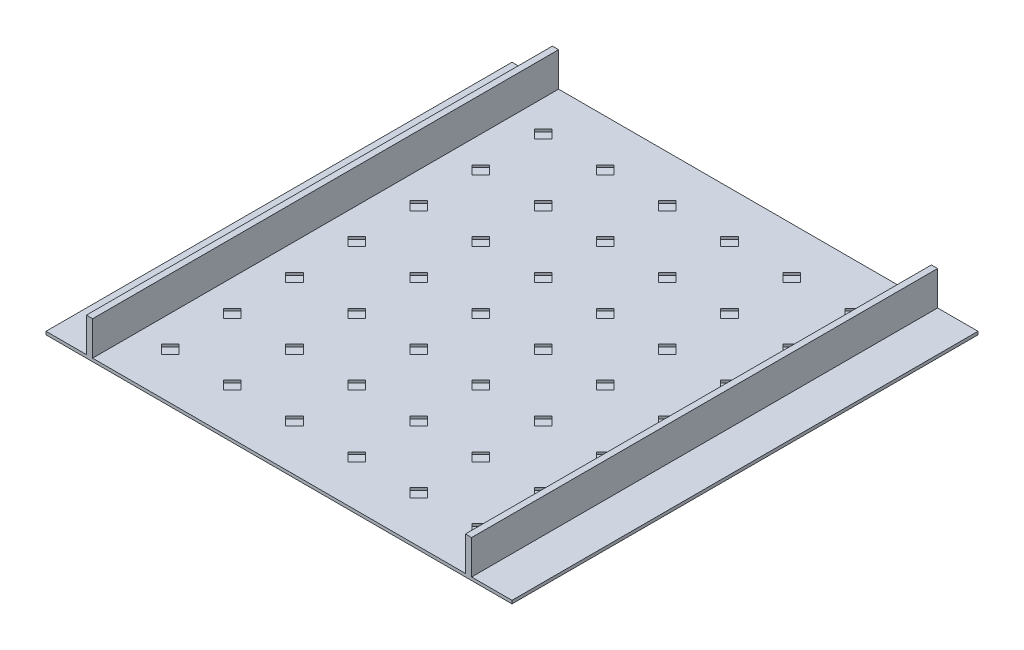
SolidWorks part; units mm, degrees
ref_plane "Front Plane" through (0, 0, 0) normal (0, 0, 1) x (1, 0, 0)
ref_plane "Top Plane" through (0, 0, 0) normal (0, 1, 0) x (1, 0, 0)
ref_plane "Right Plane" through (0, 0, 0) normal (1, 0, 0) x (0, 0, -1)
sketch "Sketch2" plane through (0, 0, 0) normal (0, 1, 0) x (1, 0, 0)
  line L1 (-750, 750) -> (750, 750)
  line L2 (-750, 750) -> (-750, -750)
  line L3 (-750, -750) -> (750, -750)
  line L4 (750, 750) -> (750, -750)
  line L5 (-750, 750) -> (750, -750) construction
  line L6 (-750, -750) -> (750, 750) construction
  point P0 (0, 0)
  dimension "D1" = 1500
  dimension "D2" = 1500
extrude "Boss-Extrude1" add sketch "Sketch2" along normal blind 10
sketch "Sketch3" plane through (0, 10, 0) normal (0, 1, 0) x (1, 0, 0)
  line L0 (620, 750) -> (620, -750) construction
  line L1 (750, 750) -> (-750, 750) construction
  line L2 (-750, -750) -> (750, -750) construction
  line L3 (600, 750) -> (600, -750) construction
  line L4 (750, -750) -> (750, 750) construction
  line L5 (-750, -600) -> (750, -600) construction
  line L6 (-750, 750) -> (-750, -750) construction
  line L7 (-750, -620) -> (750, -620) construction
  line L8 (-750, 0) -> (750, 0) construction
  line L9 (0, 750) -> (0, -750) construction
  line L10 (-750, 620) -> (750, 620) construction
  line L11 (-750, 600) -> (750, 600) construction
  line L12 (-620, 750) -> (-620, -750) construction
  line L13 (-600, 750) -> (-600, -750) construction
  line L15 (-620, 750) -> (-600, 750)
  line L16 (-620, 750) -> (-620, -750)
  line L17 (-620, -750) -> (-600, -750)
  line L18 (-600, 750) -> (-600, -750)
  line L19 (600, 750) -> (620, 750)
  line L20 (600, 750) -> (600, -750)
  line L21 (600, -750) -> (620, -750)
  line L22 (620, 750) -> (620, -750)
  dimension "D6" = 150
  dimension "D5" = 20
  dimension "D7" = 20
  dimension "D8" = 150
extrude "Boss-Extrude2" add sketch "Sketch3" along normal blind 110
sketch "Sketch4" plane through (0, 10, 0) normal (0, 1, 0) x (1, 0, 0)
  line L0 (-500, 628.2843) -> (-471.7157, 600)
  line L1 (-500, 628.2843) -> (-528.2843, 600)
  line L2 (-471.7157, 600) -> (-500, 571.7157)
  line L3 (-528.2843, 600) -> (-500, 571.7157)
  line L4 (-500, 628.2843) -> (-500, 571.7157) construction
  line L5 (-471.7157, 600) -> (-528.2843, 600) construction
  line L6 (-300, 628.2843) -> (-271.7157, 600)
  line L7 (-300, 628.2843) -> (-328.2843, 600)
  line L8 (-271.7157, 600) -> (-300, 571.7157)
  line L9 (-328.2843, 600) -> (-300, 571.7157)
  line L10 (-300, 628.2843) -> (-300, 571.7157) construction
  line L11 (-271.7157, 600) -> (-328.2843, 600) construction
  line L12 (-100, 628.2843) -> (-71.7157, 600)
  line L13 (-100, 628.2843) -> (-128.2843, 600)
  line L14 (-71.7157, 600) -> (-100, 571.7157)
  line L15 (-128.2843, 600) -> (-100, 571.7157)
  line L16 (-100, 628.2843) -> (-100, 571.7157) construction
  line L17 (-71.7157, 600) -> (-128.2843, 600) construction
  line L18 (100, 628.2843) -> (128.2843, 600)
  line L19 (100, 628.2843) -> (71.7157, 600)
  line L20 (128.2843, 600) -> (100, 571.7157)
  line L21 (71.7157, 600) -> (100, 571.7157)
  line L22 (100, 628.2843) -> (100, 571.7157) construction
  line L23 (128.2843, 600) -> (71.7157, 600) construction
  line L24 (300, 628.2843) -> (328.2843, 600)
  line L25 (300, 628.2843) -> (271.7157, 600)
  line L26 (328.2843, 600) -> (300, 571.7157)
  line L27 (271.7157, 600) -> (300, 571.7157)
  line L28 (300, 628.2843) -> (300, 571.7157) construction
  line L29 (328.2843, 600) -> (271.7157, 600) construction
  line L30 (500, 628.2843) -> (528.2843, 600)
  line L31 (500, 628.2843) -> (471.7157, 600)
  line L32 (528.2843, 600) -> (500, 571.7157)
  line L33 (471.7157, 600) -> (500, 571.7157)
  line L34 (500, 628.2843) -> (500, 571.7157) construction
  line L35 (528.2843, 600) -> (471.7157, 600) construction
  line L36 (-300, 428.2843) -> (-271.7157, 400)
  line L37 (-300, 428.2843) -> (-328.2843, 400)
  line L38 (-271.7157, 400) -> (-300, 371.7157)
  line L39 (-328.2843, 400) -> (-300, 371.7157)
  line L40 (-300, 428.2843) -> (-300, 371.7157) construction
  line L41 (-271.7157, 400) -> (-328.2843, 400) construction
  line L42 (-100, 428.2843) -> (-71.7157, 400)
  line L43 (-100, 428.2843) -> (-128.2843, 400)
  line L44 (-71.7157, 400) -> (-100, 371.7157)
  line L45 (-128.2843, 400) -> (-100, 371.7157)
  line L46 (-100, 428.2843) -> (-100, 371.7157) construction
  line L47 (-71.7157, 400) -> (-128.2843, 400) construction
  line L48 (100, 428.2843) -> (128.2843, 400)
  line L49 (100, 428.2843) -> (71.7157, 400)
  line L50 (128.2843, 400) -> (100, 371.7157)
  line L51 (71.7157, 400) -> (100, 371.7157)
  line L52 (100, 428.2843) -> (100, 371.7157) construction
  line L53 (128.2843, 400) -> (71.7157, 400) construction
  line L54 (300, 428.2843) -> (328.2843, 400)
  line L55 (300, 428.2843) -> (271.7157, 400)
  line L56 (328.2843, 400) -> (300, 371.7157)
  line L57 (271.7157, 400) -> (300, 371.7157)
  line L58 (300, 428.2843) -> (300, 371.7157) construction
  line L59 (328.2843, 400) -> (271.7157, 400) construction
  line L60 (500, 428.2843) -> (528.2843, 400)
  line L61 (500, 428.2843) -> (471.7157, 400)
  line L62 (528.2843, 400) -> (500, 371.7157)
  line L63 (471.7157, 400) -> (500, 371.7157)
  line L64 (500, 428.2843) -> (500, 371.7157) construction
  line L65 (528.2843, 400) -> (471.7157, 400) construction
  line L66 (-300, 228.2843) -> (-271.7157, 200)
  line L67 (-300, 228.2843) -> (-328.2843, 200)
  line L68 (-271.7157, 200) -> (-300, 171.7157)
  line L69 (-328.2843, 200) -> (-300, 171.7157)
  line L70 (-300, 228.2843) -> (-300, 171.7157) construction
  line L71 (-271.7157, 200) -> (-328.2843, 200) construction
  line L72 (-100, 228.2843) -> (-71.7157, 200)
  line L73 (-100, 228.2843) -> (-128.2843, 200)
  line L74 (-71.7157, 200) -> (-100, 171.7157)
  line L75 (-128.2843, 200) -> (-100, 171.7157)
  line L76 (-100, 228.2843) -> (-100, 171.7157) construction
  line L77 (-71.7157, 200) -> (-128.2843, 200) construction
  line L78 (100, 228.2843) -> (128.2843, 200)
  line L79 (100, 228.2843) -> (71.7157, 200)
  line L80 (128.2843, 200) -> (100, 171.7157)
  line L81 (71.7157, 200) -> (100, 171.7157)
  line L82 (100, 228.2843) -> (100, 171.7157) construction
  line L83 (128.2843, 200) -> (71.7157, 200) construction
  line L84 (300, 228.2843) -> (328.2843, 200)
  line L85 (300, 228.2843) -> (271.7157, 200)
  line L86 (328.2843, 200) -> (300, 171.7157)
  line L87 (271.7157, 200) -> (300, 171.7157)
  line L88 (300, 228.2843) -> (300, 171.7157) construction
  line L89 (328.2843, 200) -> (271.7157, 200) construction
  line L90 (500, 228.2843) -> (528.2843, 200)
  line L91 (500, 228.2843) -> (471.7157, 200)
  line L92 (528.2843, 200) -> (500, 171.7157)
  line L93 (471.7157, 200) -> (500, 171.7157)
  line L94 (500, 228.2843) -> (500, 171.7157) construction
  line L95 (528.2843, 200) -> (471.7157, 200) construction
  line L96 (-300, 28.2843) -> (-271.7157, 0)
  line L97 (-300, 28.2843) -> (-328.2843, 0)
  line L98 (-271.7157, 0) -> (-300, -28.2843)
  line L99 (-328.2843, 0) -> (-300, -28.2843)
  line L100 (-300, 28.2843) -> (-300, -28.2843) construction
  line L101 (-271.7157, 0) -> (-328.2843, 0) construction
  line L102 (-100, 28.2843) -> (-71.7157, 0)
  line L103 (-100, 28.2843) -> (-128.2843, 0)
  line L104 (-71.7157, 0) -> (-100, -28.2843)
  line L105 (-128.2843, 0) -> (-100, -28.2843)
  line L106 (-100, 28.2843) -> (-100, -28.2843) construction
  line L107 (-71.7157, 0) -> (-128.2843, 0) construction
  line L108 (100, 28.2843) -> (128.2843, 0)
  line L109 (100, 28.2843) -> (71.7157, 0)
  line L110 (128.2843, 0) -> (100, -28.2843)
  line L111 (71.7157, 0) -> (100, -28.2843)
  line L112 (100, 28.2843) -> (100, -28.2843) construction
  line L113 (128.2843, 0) -> (71.7157, 0) construction
  line L114 (300, 28.2843) -> (328.2843, 0)
  line L115 (300, 28.2843) -> (271.7157, 0)
  line L116 (328.2843, 0) -> (300, -28.2843)
  line L117 (271.7157, 0) -> (300, -28.2843)
  line L118 (300, 28.2843) -> (300, -28.2843) construction
  line L119 (328.2843, 0) -> (271.7157, 0) construction
  line L120 (500, 28.2843) -> (528.2843, 0)
  line L121 (500, 28.2843) -> (471.7157, 0)
  line L122 (528.2843, 0) -> (500, -28.2843)
  line L123 (471.7157, 0) -> (500, -28.2843)
  line L124 (500, 28.2843) -> (500, -28.2843) construction
  line L125 (528.2843, 0) -> (471.7157, 0) construction
  line L126 (-300, -171.7157) -> (-271.7157, -200)
  line L127 (-300, -171.7157) -> (-328.2843, -200)
  line L128 (-271.7157, -200) -> (-300, -228.2843)
  line L129 (-328.2843, -200) -> (-300, -228.2843)
  line L130 (-300, -171.7157) -> (-300, -228.2843) construction
  line L131 (-271.7157, -200) -> (-328.2843, -200) construction
  line L132 (-100, -171.7157) -> (-71.7157, -200)
  line L133 (-100, -171.7157) -> (-128.2843, -200)
  line L134 (-71.7157, -200) -> (-100, -228.2843)
  line L135 (-128.2843, -200) -> (-100, -228.2843)
  line L136 (-100, -171.7157) -> (-100, -228.2843) construction
  line L137 (-71.7157, -200) -> (-128.2843, -200) construction
  line L138 (100, -171.7157) -> (128.2843, -200)
  line L139 (100, -171.7157) -> (71.7157, -200)
  line L140 (128.2843, -200) -> (100, -228.2843)
  line L141 (71.7157, -200) -> (100, -228.2843)
  line L142 (100, -171.7157) -> (100, -228.2843) construction
  line L143 (128.2843, -200) -> (71.7157, -200) construction
  line L144 (300, -171.7157) -> (328.2843, -200)
  line L145 (300, -171.7157) -> (271.7157, -200)
  line L146 (328.2843, -200) -> (300, -228.2843)
  line L147 (271.7157, -200) -> (300, -228.2843)
  line L148 (300, -171.7157) -> (300, -228.2843) construction
  line L149 (328.2843, -200) -> (271.7157, -200) construction
  line L150 (500, -171.7157) -> (528.2843, -200)
  line L151 (500, -171.7157) -> (471.7157, -200)
  line L152 (528.2843, -200) -> (500, -228.2843)
  line L153 (471.7157, -200) -> (500, -228.2843)
  line L154 (500, -171.7157) -> (500, -228.2843) construction
  line L155 (528.2843, -200) -> (471.7157, -200) construction
  line L156 (-300, -371.7157) -> (-271.7157, -400)
  line L157 (-300, -371.7157) -> (-328.2843, -400)
  line L158 (-271.7157, -400) -> (-300, -428.2843)
  line L159 (-328.2843, -400) -> (-300, -428.2843)
  line L160 (-300, -371.7157) -> (-300, -428.2843) construction
  line L161 (-271.7157, -400) -> (-328.2843, -400) construction
  line L162 (-100, -371.7157) -> (-71.7157, -400)
  line L163 (-100, -371.7157) -> (-128.2843, -400)
  line L164 (-71.7157, -400) -> (-100, -428.2843)
  line L165 (-128.2843, -400) -> (-100, -428.2843)
  line L166 (-100, -371.7157) -> (-100, -428.2843) construction
  line L167 (-71.7157, -400) -> (-128.2843, -400) construction
  line L168 (100, -371.7157) -> (128.2843, -400)
  line L169 (100, -371.7157) -> (71.7157, -400)
  line L170 (128.2843, -400) -> (100, -428.2843)
  line L171 (71.7157, -400) -> (100, -428.2843)
  line L172 (100, -371.7157) -> (100, -428.2843) construction
  line L173 (128.2843, -400) -> (71.7157, -400) construction
  line L174 (300, -371.7157) -> (328.2843, -400)
  line L175 (300, -371.7157) -> (271.7157, -400)
  line L176 (328.2843, -400) -> (300, -428.2843)
  line L177 (271.7157, -400) -> (300, -428.2843)
  line L178 (300, -371.7157) -> (300, -428.2843) construction
  line L179 (328.2843, -400) -> (271.7157, -400) construction
  line L180 (500, -371.7157) -> (528.2843, -400)
  line L181 (500, -371.7157) -> (471.7157, -400)
  line L182 (528.2843, -400) -> (500, -428.2843)
  line L183 (471.7157, -400) -> (500, -428.2843)
  line L184 (500, -371.7157) -> (500, -428.2843) construction
  line L185 (528.2843, -400) -> (471.7157, -400) construction
  line L186 (-500, 428.2843) -> (-471.7157, 400)
  line L187 (-500, 428.2843) -> (-528.2843, 400)
  line L188 (-471.7157, 400) -> (-500, 371.7157)
  line L189 (-528.2843, 400) -> (-500, 371.7157)
  line L190 (-500, 428.2843) -> (-500, 371.7157) construction
  line L191 (-471.7157, 400) -> (-528.2843, 400) construction
  line L192 (-500, 228.2843) -> (-471.7157, 200)
  line L193 (-500, 228.2843) -> (-528.2843, 200)
  line L194 (-471.7157, 200) -> (-500, 171.7157)
  line L195 (-528.2843, 200) -> (-500, 171.7157)
  line L196 (-500, 228.2843) -> (-500, 171.7157) construction
  line L197 (-471.7157, 200) -> (-528.2843, 200) construction
  line L198 (-500, 28.2843) -> (-471.7157, 0)
  line L199 (-500, 28.2843) -> (-528.2843, 0)
  line L200 (-471.7157, 0) -> (-500, -28.2843)
  line L201 (-528.2843, 0) -> (-500, -28.2843)
  line L202 (-500, 28.2843) -> (-500, -28.2843) construction
  line L203 (-471.7157, 0) -> (-528.2843, 0) construction
  line L204 (-500, -171.7157) -> (-471.7157, -200)
  line L205 (-500, -171.7157) -> (-528.2843, -200)
  line L206 (-471.7157, -200) -> (-500, -228.2843)
  line L207 (-528.2843, -200) -> (-500, -228.2843)
  line L208 (-500, -171.7157) -> (-500, -228.2843) construction
  line L209 (-471.7157, -200) -> (-528.2843, -200) construction
  line L210 (-500, -371.7157) -> (-471.7157, -400)
  line L211 (-500, -371.7157) -> (-528.2843, -400)
  line L212 (-471.7157, -400) -> (-500, -428.2843)
  line L213 (-528.2843, -400) -> (-500, -428.2843)
  line L214 (-500, -371.7157) -> (-500, -428.2843) construction
  line L215 (-471.7157, -400) -> (-528.2843, -400) construction
  line L216 (0, 750) -> (0, -750) construction
  line L217 (600, 750) -> (-600, 750) construction
  line L218 (-600, -750) -> (600, -750) construction
  line L219 (-750, 0) -> (750, 0) construction
  line L220 (-750, 750) -> (-750, -750) construction
  line L221 (750, -750) -> (750, 750) construction
  line L222 (-100, 600) -> (100, 600) construction
  line L223 (-100, -400) -> (100, -400) construction
  line L224 (0, -400) -> (0, 600) construction
  line L225 (-500, -571.7157) -> (-471.7157, -600)
  line L226 (-500, -571.7157) -> (-528.2843, -600)
  line L227 (-471.7157, -600) -> (-500, -628.2843)
  line L228 (-528.2843, -600) -> (-500, -628.2843)
  line L229 (-500, -571.7157) -> (-500, -628.2843) construction
  line L230 (-471.7157, -600) -> (-528.2843, -600) construction
  line L231 (-300, -571.7157) -> (-271.7157, -600)
  line L232 (-300, -571.7157) -> (-328.2843, -600)
  line L233 (-271.7157, -600) -> (-300, -628.2843)
  line L234 (-328.2843, -600) -> (-300, -628.2843)
  line L235 (-300, -571.7157) -> (-300, -628.2843) construction
  line L236 (-271.7157, -600) -> (-328.2843, -600) construction
  line L237 (-100, -571.7157) -> (-71.7157, -600)
  line L238 (-100, -571.7157) -> (-128.2843, -600)
  line L239 (-71.7157, -600) -> (-100, -628.2843)
  line L240 (-128.2843, -600) -> (-100, -628.2843)
  line L241 (-100, -571.7157) -> (-100, -628.2843) construction
  line L242 (-71.7157, -600) -> (-128.2843, -600) construction
  line L243 (100, -571.7157) -> (128.2843, -600)
  line L244 (100, -571.7157) -> (71.7157, -600)
  line L245 (128.2843, -600) -> (100, -628.2843)
  line L246 (71.7157, -600) -> (100, -628.2843)
  line L247 (100, -571.7157) -> (100, -628.2843) construction
  line L248 (128.2843, -600) -> (71.7157, -600) construction
  line L249 (300, -571.7157) -> (328.2843, -600)
  line L250 (300, -571.7157) -> (271.7157, -600)
  line L251 (328.2843, -600) -> (300, -628.2843)
  line L252 (271.7157, -600) -> (300, -628.2843)
  line L253 (300, -571.7157) -> (300, -628.2843) construction
  line L254 (328.2843, -600) -> (271.7157, -600) construction
  line L255 (500, -571.7157) -> (528.2843, -600)
  line L256 (500, -571.7157) -> (471.7157, -600)
  line L257 (528.2843, -600) -> (500, -628.2843)
  line L258 (471.7157, -600) -> (500, -628.2843)
  line L259 (500, -571.7157) -> (500, -628.2843) construction
  line L260 (528.2843, -600) -> (471.7157, -600) construction
  point P1 (-500, 600)
  point P3 (-300, 600)
  point P12 (-100, 600)
  point P17 (100, 600)
  point P22 (300, 600)
  point P27 (500, 600)
  point P32 (-300, 400)
  point P37 (-100, 400)
  point P42 (100, 400)
  point P47 (300, 400)
  point P52 (500, 400)
  point P57 (-300, 200)
  point P62 (-100, 200)
  point P67 (100, 200)
  point P72 (300, 200)
  point P77 (500, 200)
  point P82 (-300, 0)
  point P87 (-100, 0)
  point P92 (100, 0)
  point P97 (300, 0)
  point P102 (500, 0)
  point P107 (-300, -200)
  point P112 (-100, -200)
  point P117 (100, -200)
  point P122 (300, -200)
  point P127 (500, -200)
  point P132 (-300, -400)
  point P137 (-100, -400)
  point P142 (100, -400)
  point P147 (300, -400)
  point P152 (500, -400)
  point P157 (-500, 400)
  point P162 (-500, 200)
  point P167 (-500, 0)
  point P172 (-500, -200)
  point P177 (-500, -400)
  point P198 (-500, -600)
  point P205 (-300, -600)
  point P210 (-100, -600)
  point P215 (100, -600)
  point P220 (300, -600)
  point P225 (500, -600)
  dimension "D1" = 40
  dimension "D2" = 40
  dimension "D5" = 200
  dimension "D6" = 200
  dimension "D3" = 6
  dimension "D4" = 7
extrude "Cut-Extrude1" cut sketch "Sketch4" against normal blind 8
equation "\"CellSize\"=1500"
equation "\"D1@Sketch2\"=\"CellSize\""
equation "\"D2@Sketch2\"=\"CellSize\""
equation "\"TrackWidth\"= 1200"
equation "\"C\"=342.079"
equation "\"WallWidth\"=20"
equation "\"D6@Sketch3\"=\"EdgeWidth\""
equation "\"D5@Sketch3\"=\"WallWidth\""
equation "\"D7@Sketch3\"=\"WallWidth\""
equation "\"EdgeWidth\"= ( \"CellSize\" - \"TrackWidth\" ) / 2"
equation "\"D8@Sketch3\"=\"EdgeWidth\""
equation "\"HoleWidth\"=40"
equation "\"D1@Sketch4\"=\"HoleWidth\""
equation "\"D2@Sketch4\"=\"HoleWidth\""
